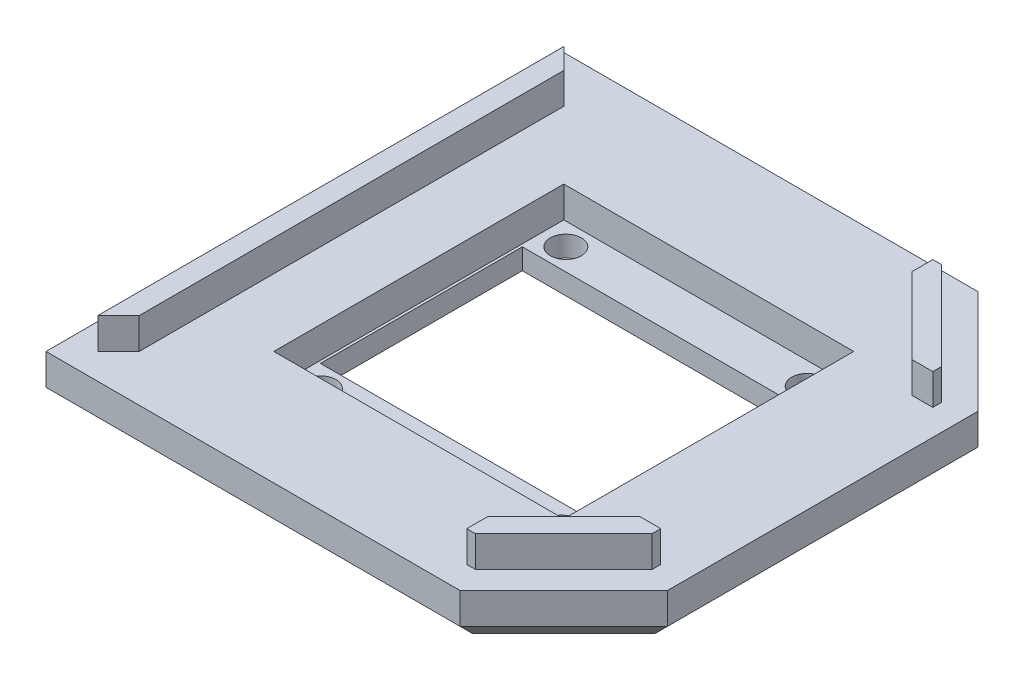
SolidWorks part; units mm, degrees
ref_plane "Front Plane" through (0, 0, 0) normal (0, 0, 1) x (1, 0, 0)
ref_plane "Top Plane" through (0, 0, 0) normal (0, 1, 0) x (1, 0, 0)
ref_plane "Right Plane" through (0, 0, 0) normal (1, 0, 0) x (0, 0, -1)
sketch "Sketch1" plane through (0, 0, 0) normal (0, 1, 0) x (1, 0, 0)
  line L0 (15, 25) -> (25, 15)
  line L1 (-25, 25) -> (15, 25)
  line L2 (-25, 25) -> (-25, -25)
  line L3 (-25, -25) -> (15, -25)
  line L4 (25, 15) -> (25, -15)
  line L5 (0, -25) -> (0, 25) construction
  line L6 (-25, 0) -> (25, 0) construction
  line L7 (15, -25) -> (25, -15)
  point P0 (0, 0)
  point P1 (25, -25)
  point P8 (25, 25)
  dimension "D1" = 50
  dimension "D2" = 50
extrude "Boss-Extrude1" add sketch "Sketch1" along normal blind 5
sketch "Sketch2" plane through (0, 5, 0) normal (0, 1, 0) x (1, 0, 0)
  line L18 (-22.5, 22.5) -> (-22.5, -22.5)
  line L19 (-22.5, -22.5) -> (13.9645, -22.5)
  line L20 (13.9645, -22.5) -> (22.5, -13.9645)
  line L21 (22.5, -13.9645) -> (22.5, 13.9645)
  line L22 (22.5, 13.9645) -> (13.9645, 22.5)
  line L23 (13.9645, 22.5) -> (-22.5, 22.5)
  line L24 (-22.5, 22.5) -> (-22.5, -22.5)
  line L25 (-22.5, -22.5) -> (13.9645, -22.5)
  line L26 (13.9645, -22.5) -> (22.5, -13.9645)
  line L27 (22.5, -13.9645) -> (22.5, 13.9645)
  line L28 (22.5, 13.9645) -> (13.9645, 22.5)
  line L29 (13.9645, 22.5) -> (-22.5, 22.5)
  line L30 (20.5, -13.136) -> (22.5, -13.136)
  line L31 (13.136, -20.5) -> (13.136, -22.5)
  line L32 (-22.5, 22.5) -> (-20.5, 20.5)
  line L33 (-20.5, 20.5) -> (-20.4742, 20.4792)
  line L34 (-22.5, -22.5) -> (-20.5, -20.5)
  line L35 (13.136, 20.5) -> (13.136, 22.5)
  line L36 (-20.5, 20.5) -> (-20.5, -20.5)
  line L37 (-20.5, -20.5) -> (13.136, -20.5)
  line L38 (13.136, -20.5) -> (20.5, -13.136)
  line L39 (20.5, -13.136) -> (20.5, 13.136)
  line L40 (20.5, 13.136) -> (13.136, 20.5)
  line L41 (13.136, 20.5) -> (-20.5, 20.5)
  line L42 (-20.5, 20.5) -> (-20.5, -20.5)
  line L43 (-20.5, -20.5) -> (13.136, -20.5)
  line L44 (13.136, -20.5) -> (20.5, -13.136)
  line L45 (20.5, -13.136) -> (20.5, 13.136)
  line L46 (20.5, 13.136) -> (13.136, 20.5)
  line L47 (13.136, 20.5) -> (-20.5, 20.5)
  line L48 (20.5, 13.136) -> (22.5, 13.136)
  point P0 (0, 0)
  dimension "D1" = 2.5
  dimension "D2" = 4.5
extrude "Boss-Extrude2" add sketch "Sketch2" along normal blind 3 contours L42 L32 L24 L34 | L46 L48 L27 L28 L29 L35 | L44 L31 L25 L26 L27 L30
chamfer "Chamfer1" distance 2 angle 45 6 edges at (-5, 0, -25) (-25, 0, 0) (-5, 0, 25) (20, 0, 20) (25, 0, 0) (20, 0, -20)
sketch "Sketch4" plane through (0, 0, 0) normal (0, -1, 0) x (-1, 0, 0)
  line L1 (-13.75, 9.75) -> (13.75, 9.75)
  line L2 (-13.75, 9.75) -> (-13.75, -9.75)
  line L3 (-13.75, -9.75) -> (13.75, -9.75)
  line L4 (13.75, 9.75) -> (13.75, -9.75)
  line L5 (0, -9.75) -> (0, 9.75) construction
  line L6 (-13.75, 0) -> (13.75, 0) construction
  circle A0 centre (-11.65, -11.85) radius 1.5
  circle A1 centre (11.65, -11.85) radius 1.5
  circle A2 centre (11.65, 11.85) radius 1.5
  circle A3 centre (-11.65, 11.85) radius 1.5
  point P0 (0, 0)
  dimension "D3" = 3
  dimension "D1" = 27.5
  dimension "D2" = 19.5
  dimension "D4" = 2.1
  dimension "D5" = 2.1
extrude "Cut-Extrude2" cut sketch "Sketch4" against normal blind 8
sketch "Sketch5" plane through (0, 5, 0) normal (0, 1, 0) x (1, 0, 0)
  line L1 (-14, -14) -> (14, -14)
  line L2 (-14, -14) -> (-14, 14)
  line L3 (-14, 14) -> (14, 14)
  line L4 (14, -14) -> (14, 14)
  line L5 (0, 14) -> (0, -14) construction
  line L6 (-14, 0) -> (14, 0) construction
  point P0 (0, 0)
  dimension "D1" = 28
  dimension "D2" = 28
extrude "Cut-Extrude3" cut sketch "Sketch5" against normal blind 3
